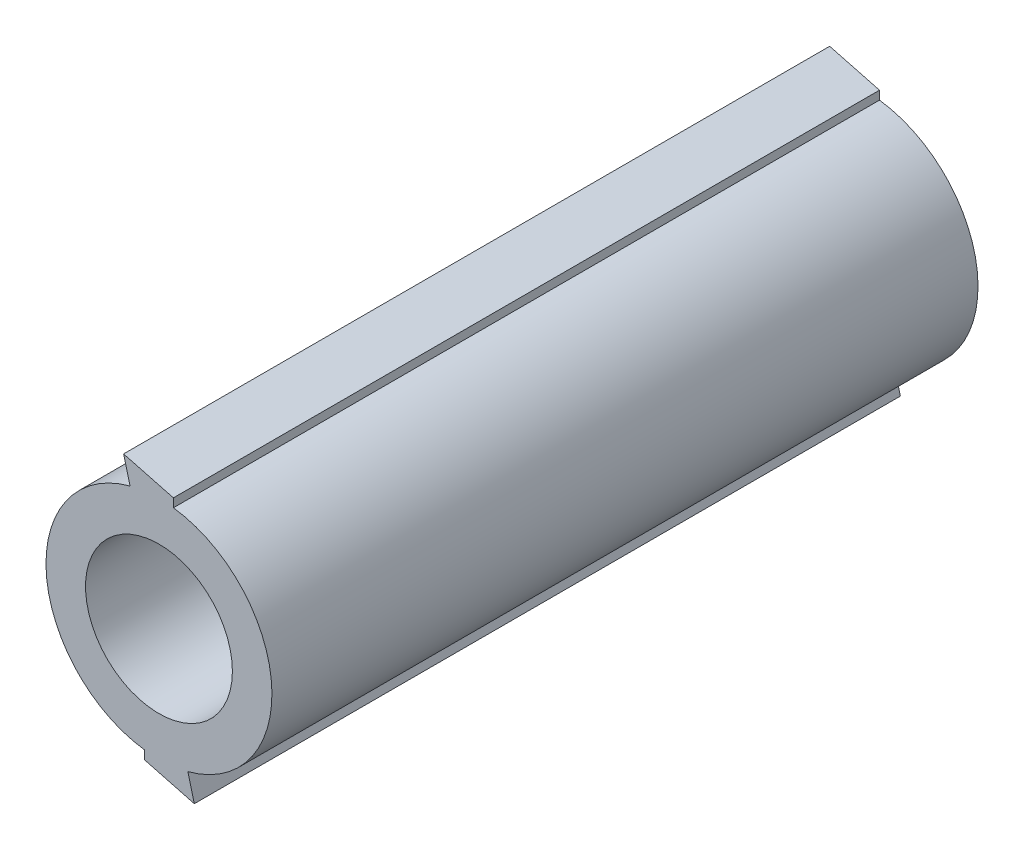
SolidWorks part; units mm, degrees
ref_plane "Front Plane" through (0, 0, 0) normal (0, 0, 1) x (1, 0, 0)
ref_plane "Top Plane" through (0, 0, 0) normal (0, 1, 0) x (1, 0, 0)
ref_plane "Right Plane" through (0, 0, 0) normal (1, 0, 0) x (0, 0, -1)
sketch "Sketch1" plane through (0, 0, 0) normal (0, 0, 1) x (1, 0, 0)
  line L0 (0, 45.1908) -> (0, -44.5528) construction
  line L1 (-67.9507, 0) -> (57.602, 0) construction
  line L2 (0, 40) -> (0.0001, 40) construction
  line L3 (0, 40) -> (0, 26)
  circle A0 centre (0, 0) radius 40
  circle A1 centre (0, 0) radius 26
  circle A3 centre (28.5788, 16.5) radius 4
  circle A4 centre (28.5788, -16.5) radius 4
  circle A5 centre (0, -33) radius 4
  circle A6 centre (-28.5788, -16.5) radius 4
  circle A7 centre (-28.5788, 16.5) radius 4
  point P10 (0, 33)
  point P27 (0, 0)
extrude "Boss-Extrude1" add sketch "Sketch1" along normal blind 200
sketch "Sketch3" plane through (0, 0, 0) normal (0, 0, -1) x (-1, 0, 0)
  line L0 (0, 50.759) -> (0, -44.8075) construction
  line L1 (-76.4333, 0) -> (51.9225, 0) construction
  circle A0 centre (0, 33) radius 4
  circle A1 centre (28.5788, 16.5) radius 4
  circle A2 centre (28.5788, -16.5) radius 4
  circle A3 centre (0, -33) radius 4
  circle A4 centre (-28.5788, -16.5) radius 4
  circle A5 centre (-28.5788, 16.5) radius 4
  point P5 (0, 33)
  point P20 (0, 0)
  dimension "D2" = 6
  dimension "D1" = 33
extrude "Cut-Extrude1" cut sketch "Sketch3" against normal blind 10 contours A0 | A5 | A4 | A3 | A2 | A1
sketch "Sketch4" plane through (0, 0, 200) normal (0, 0, 1) x (1, 0, 0)
  line L0 (-10.2239, 38.6713) -> (-12.5243, 47.3724)
  line L1 (-12.5243, 47.3724) -> (5.1174, 42.7273)
  line L2 (5.1174, 42.7273) -> (5.1174, 39.6713)
  line L3 (-5.1174, -42.7273) -> (-5.1174, -39.6713)
  line L4 (10.2239, -38.6713) -> (12.5243, -47.3724)
  line L5 (12.5243, -47.3724) -> (-5.1174, -42.7273)
  arc A0 (-10.2239, 38.6713) -> (5.1174, 39.6713) centre (0, 0) ccw
  circle A1 centre (0, 0) radius 40 construction
  arc A2 (10.2239, -38.6713) -> (-5.1174, -39.6713) centre (0, 0) ccw
  point P15 (0, 0)
  circle M10 centre (0, 0) radius 40
  dimension "D1" = 9
  dimension "D2" = 2
extrude "Boss-Extrude2" add sketch "Sketch4" against normal blind 200 contours L2 L1 L0 M10 | L5 L4 L3 M10
scale "Scale3" scale about centroid uniform scaling no x scale factor 0.8 y scale factor 0.8 z scale factor 1
